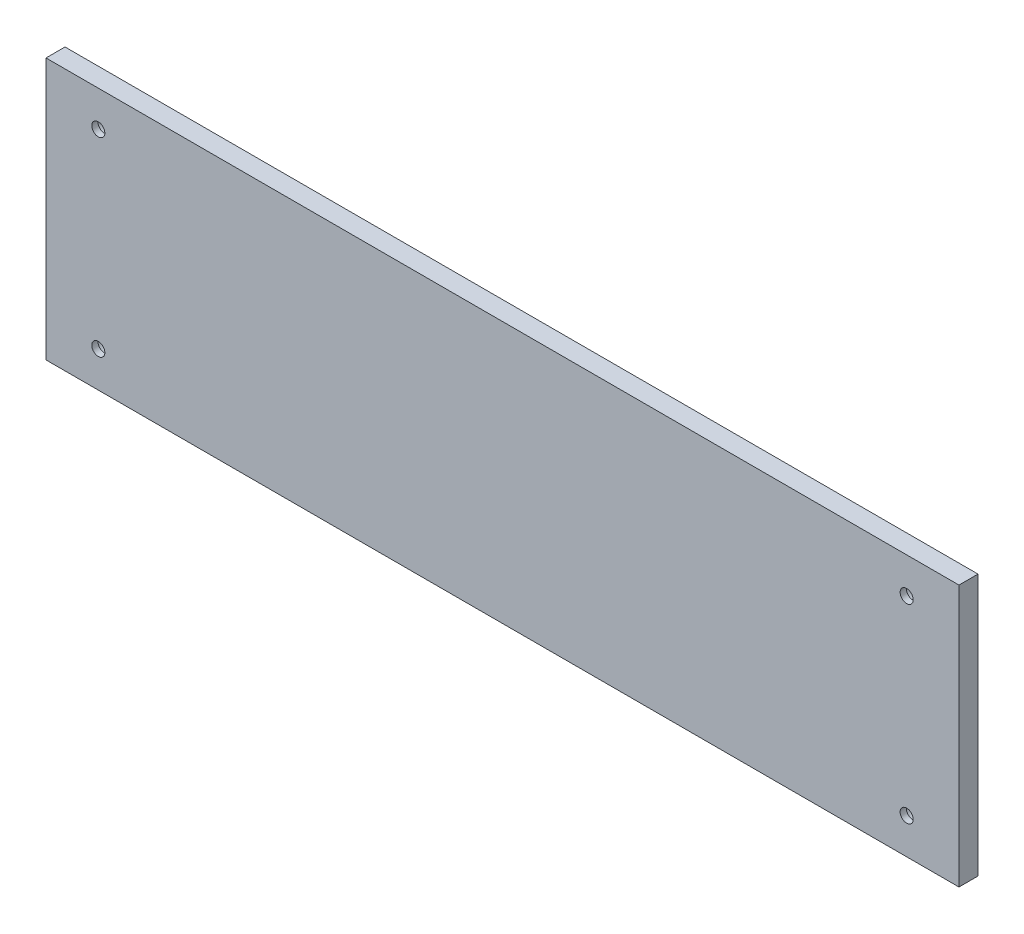
SolidWorks part; units mm, degrees
ref_plane "Front Plane" through (0, 0, 0) normal (0, 0, 1) x (1, 0, 0)
ref_plane "Top Plane" through (0, 0, 0) normal (0, 1, 0) x (1, 0, 0)
ref_plane "Right Plane" through (0, 0, 0) normal (1, 0, 0) x (0, 0, -1)
sketch "Sketch1" plane through (0, 0, 0) normal (0, 0, 1) x (1, 0, 0)
  line L1 (0, 0) -> (384, 0)
  line L2 (0, 0) -> (0, 110)
  line L3 (0, 110) -> (384, 110)
  line L4 (384, 0) -> (384, 110)
extrude "Extrude2" add sketch "Sketch1" along normal blind 8
sketch "Sketch3" plane through (0, 0, 0) normal (0, 0, -1) x (-1, 0, 0)
  line L0 (-362, 95) -> (-22, 95) construction
  line L1 (-22, 95) -> (-22, 15) construction
  line L2 (-22, 15) -> (-362, 15) construction
  line L3 (-362, 15) -> (-362, 95) construction
hole_wizard "CBORE for M5 Hex Socket Head Cap Screw1" positions "3DSketch1" profile "Sketch5" counterbore size "M5" standard "DIN" end condition through all
sketch3d "3DSketch1"
  point P0 (362, 95, 0)
  point P3 (22, 95, 0)
  point P6 (22, 15, 0)
  point P9 (362, 15, 0)
sketch "Sketch5" plane through (362, 95, 0) normal (1, 0, 0) x (0, 1, 0)
  line L0 (0, 0) -> (0, 8)
  line L1 (0, 8) -> (2.75, 8)
  line L3 (2.75, 8) -> (2.75, 5.4)
  line L4 (2.75, 5.4) -> (5, 5.4)
  line L5 (5, 5.4) -> (5, 0)
  line L7 (5, 0) -> (0, 0)
  line L11 (0, -6.35) -> (0, 107.95) construction
  dimension "Thru Hole Dia." = 5.5
  dimension "Thru Hole Depth" = 8
  dimension "C'Bore Dia." = 10
  dimension "C'Bore Depth" = 5.4
